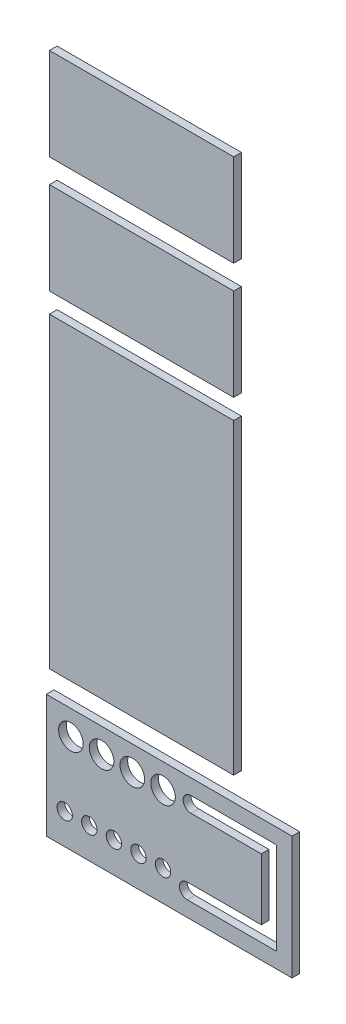
SolidWorks part; units mm, degrees
material "Maple"
ref_plane "Wasteboard" through (0, 0, 0) normal (0, 0, 1) x (1, 0, 0)
ref_plane "Left-Right" through (0, 0, 0) normal (0, 1, 0) x (1, 0, 0)
ref_plane "Front-Back" through (0, 0, 0) normal (1, 0, 0) x (0, 0, -1)
sketch "Sketch3" plane through (0, 0, 0) normal (0, 0, 1) x (1, 0, 0)
  line L1 (0, 0) -> (711.2, 0)
  line L2 (0, 0) -> (0, 304.8)
  line L3 (0, 304.8) -> (711.2, 304.8)
  line L4 (711.2, 0) -> (711.2, 304.8)
  dimension "D1" = 711.2
  dimension "D2" = 304.8
sketch "Sketch4" plane through (0, 0, 0) normal (0, 0, 1) x (1, 0, 0)
  line L0 (6.2358, 29.2255) -> (107.8358, 29.2255) construction
  line L1 (6.2358, 3.8255) -> (107.8358, 3.8255)
  line L2 (6.2358, 3.8255) -> (6.2358, 54.6255)
  line L3 (6.2358, 54.6255) -> (107.8358, 54.6255)
  line L4 (107.8358, 3.8255) -> (107.8358, 54.6255)
  line L9 (64.4666, 16.5255) -> (95.1358, 16.5255)
  line L10 (95.1358, 16.5255) -> (95.1358, 41.9255)
  line L11 (95.1358, 41.9255) -> (66.0048, 41.9255)
  line L13 (66.0048, 48.2755) -> (101.4858, 48.2755)
  line L14 (101.4858, 48.2755) -> (101.4858, 10.1755)
  line L15 (101.4858, 10.1755) -> (64.4666, 10.1755)
  line L18 (7.525, 191.3871) -> (83.725, 191.3871)
  line L19 (7.525, 191.3871) -> (7.525, 64.3871)
  line L20 (7.525, 64.3871) -> (83.725, 64.3871)
  line L21 (83.725, 191.3871) -> (83.725, 64.3871)
  line L22 (7.525, 285.7977) -> (83.725, 285.7977)
  line L23 (7.525, 285.7977) -> (7.525, 247.6977)
  line L24 (7.525, 247.6977) -> (83.725, 247.6977)
  line L25 (83.725, 285.7977) -> (83.725, 247.6977)
  line L26 (7.525, 237.7524) -> (83.725, 237.7524)
  line L27 (7.525, 237.7524) -> (7.525, 199.6524)
  line L28 (7.525, 199.6524) -> (83.725, 199.6524)
  line L29 (83.725, 237.7524) -> (83.725, 199.6524)
  circle A0 centre (13.8558, 16.5255) radius 3.175
  circle A1 centre (24.0158, 16.5255) radius 3.175
  circle A2 centre (34.1758, 16.5255) radius 3.175
  circle A3 centre (44.3358, 16.5255) radius 3.175
  circle A4 centre (54.4958, 16.5255) radius 3.175
  circle A5 centre (16.3958, 44.4655) radius 5.08
  circle A6 centre (29.0958, 44.4655) radius 5.08
  circle A7 centre (41.7958, 44.4655) radius 5.08
  circle A8 centre (54.4958, 44.4655) radius 5.08
  arc A9 (64.4666, 16.5255) -> (64.4666, 10.1755) centre (64.4666, 13.3505) ccw
  arc A10 (66.0048, 41.9255) -> (66.0048, 48.2755) centre (66.0048, 45.1005) cw
  dimension "D1" = 6.35
  dimension "D8" = 10.16
  dimension "D2" = 101.6
  dimension "D4" = 7.62
  dimension "D5" = 12.7
  dimension "D6" = 127
  dimension "D7" = 50.8
  dimension "D9" = 10.16
  dimension "D10" = 10.16
  dimension "D12" = 6.35
  dimension "D13" = 6.35
  dimension "D14" = 6.35
  dimension "D15" = 6.35
  dimension "D16" = 6.35
  dimension "D17" = 6.35
  dimension "D18" = 76.2
  dimension "D19" = 76.2
  dimension "D20" = 76.2
  dimension "D21" = 38.1
  dimension "D22" = 38.1
  dimension "D3" = 5
  dimension "D11" = 4
extrude "Boss-Extrude1" add sketch "Sketch4" along normal blind 3.175
